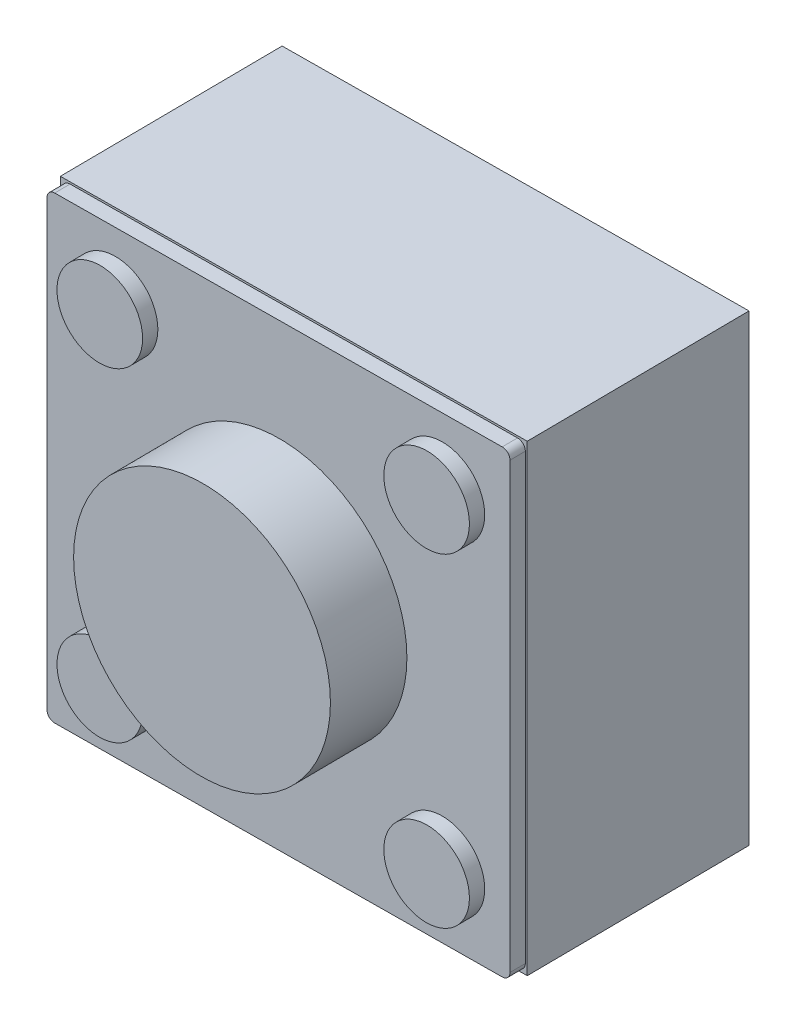
SolidWorks part; units mm, degrees
ref_plane "Front Plane" through (0, 0, 0) normal (0, 0, 1) x (1, 0, 0)
ref_plane "Top Plane" through (0, 0, 0) normal (0, 1, 0) x (1, 0, 0)
ref_plane "Right Plane" through (0, 0, 0) normal (1, 0, 0) x (0, 0, -1)
sketch "Sketch1" plane through (0, 0, 0) normal (0, 0, 1) x (1, 0, 0)
  line L1 (0, 0) -> (-5.95, 0)
  line L2 (0, 0) -> (0, -5.95)
  line L3 (0, -5.95) -> (-5.95, -5.95)
  line L4 (-5.95, 0) -> (-5.95, -5.95)
  dimension "D1" = 5.95
extrude "Boss-Extrude1" add sketch "Sketch1" along normal mid plane 0.2
sketch "Sketch2" plane through (0, 0, 0) normal (0, 0, 1) x (1, 0, 0)
  line L0 (-5.95, 0) -> (-5.95, -5.95) construction
  line L1 (-5.975, -5.975) -> (0.025, -5.975)
  line L2 (-5.975, -5.975) -> (-5.975, 0.025)
  line L3 (-5.975, 0.025) -> (0.025, 0.025)
  line L4 (0.025, -5.975) -> (0.025, 0.025)
  line L5 (-5.95, -5.95) -> (0, -5.95) construction
  point P8 (-5.95, -2.975)
  point P9 (-5.975, -2.975)
  point P12 (-2.975, -5.95)
  point P13 (-2.975, -5.975)
  dimension "D1" = 6
extrude "Boss-Extrude2" add sketch "Sketch2" along normal blind 2.9 from surface at 0.1 starting at face at (-2.975, -2.975, 0.1)
fillet "Fillet1" radius 0.1 4 edges at (-5.95, -5.95, 0) (0, -5.95, 0) (0, 0, 0) (-5.95, 0, 0)
sketch "Sketch3" plane through (0, 0, 0) normal (0, 0, 1) x (1, 0, 0)
  line L0 (-0.1, 0) -> (-5.85, 0) construction
  line L1 (-5.95, -0.1) -> (-5.95, -5.85) construction
  line L2 (-0.875, -0.875) -> (-2.975, -2.975) construction
  line L3 (-2.975, -2.975) -> (-0.875, -5.075) construction
  line L4 (-2.975, -2.975) -> (-5.075, -5.075) construction
  circle A0 centre (-2.975, -2.975) radius 1.65
  circle A1 centre (-5.075, -0.875) radius 0.55
  circle A2 centre (-5.075, -5.075) radius 0.55
  circle A3 centre (-0.875, -5.075) radius 0.55
  circle A4 centre (-0.875, -0.875) radius 0.55
  point P16 (-2.975, 0)
  point P19 (-5.95, -2.975)
  dimension "D1" = 1.1
  dimension "D2" = 3.3
  dimension "D3" = 4.2
extrude "Boss-Extrude3" add sketch "Sketch3" against normal blind 0.2 from surface at -0.1 starting at face at (-2.975, -2.975, -0.1)
sketch "Sketch4" plane through (0, 0, 0) normal (0, 0, 1) x (1, 0, 0)
  line L0 (-0.1, 0) -> (-5.85, 0) construction
  line L1 (0, -5.85) -> (0, -0.1) construction
  circle A0 centre (-2.975, -2.975) radius 1.65
  point P5 (-2.975, 0)
  point P8 (0, -2.975)
  dimension "D1" = 3.3
extrude "Boss-Extrude4" add sketch "Sketch4" against normal blind 1 from surface at -0.1 starting at face at (-1.425, -0.875, -0.1)
move or copy body "Body-Move/Copy1" bodies to move or copy 104 copy no rotation origin (-2.975, 0, 0.95) rotation axis (0, -1, 0) rotation angle 179.5
